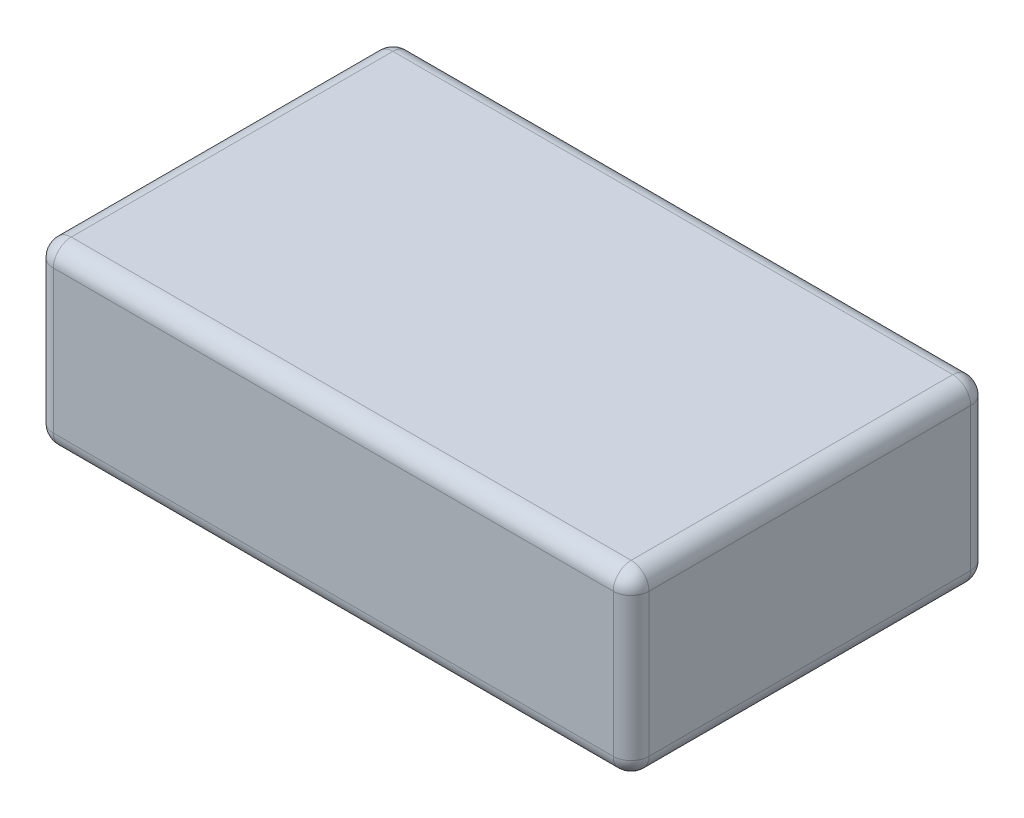
SolidWorks part; units mm, degrees
ref_plane "Спереди" through (0, 0, 0) normal (0, 0, 1) x (1, 0, 0)
ref_plane "Сверху" through (0, 0, 0) normal (0, 1, 0) x (1, 0, 0)
ref_plane "Справа" through (0, 0, 0) normal (1, 0, 0) x (0, 0, -1)
sketch "Эскиз1" plane through (0, 0, 0) normal (0, 1, 0) x (1, 0, 0)
  line L1 (-50, -30) -> (50, -30)
  line L2 (-50, -30) -> (-50, 30)
  line L3 (-50, 30) -> (50, 30)
  line L4 (50, -30) -> (50, 30)
  line L5 (0, 30) -> (0, -30) construction
  line L6 (-50, 0) -> (50, 0) construction
  point P0 (0, 0)
  dimension "D1" = 100
  dimension "D2" = 60
extrude "Бобышка-Вытянуть1" add sketch "Эскиз1" along normal blind 30
fillet "Скругление1" radius 3 12 edges at (-50, 15, -30) (-50, 15, 30) (50, 0, 0) (50, 30, 0) (0, 0, -30) (0, 30, -30) (0, 0, 30) (0, 30, 30) (-50, 30, 0) (50, 15, 30) (50, 15, -30) (-50, 0, 0)
